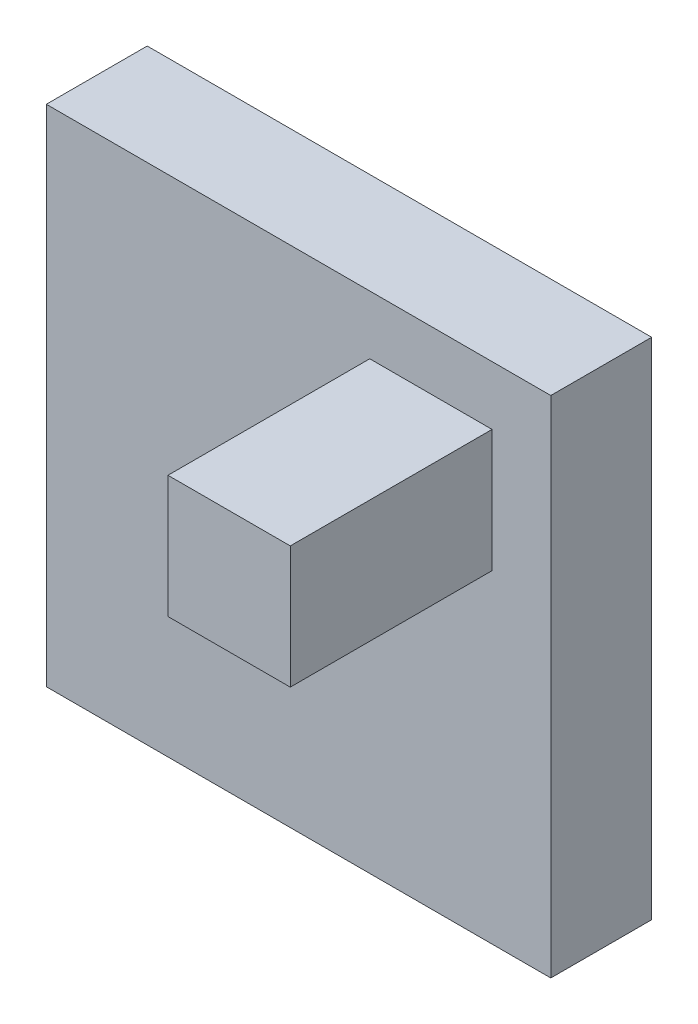
SolidWorks part; units mm, degrees
ref_plane "Front Plane" through (0, 0, 0) normal (0, 0, 1) x (1, 0, 0)
ref_plane "Top Plane" through (0, 0, 0) normal (0, 1, 0) x (1, 0, 0)
ref_plane "Right Plane" through (0, 0, 0) normal (1, 0, 0) x (0, 0, -1)
sketch "Sketch1" plane through (0, 0, 0) normal (0, 0, 1) x (1, 0, 0)
  line L1 (0, 0) -> (10, 0)
  line L2 (0, 0) -> (0, -10)
  line L3 (0, -10) -> (10, -10)
  line L4 (10, 0) -> (10, -10)
  dimension "D1" = 10
extrude "Boss-Extrude1" add sketch "Sketch1" along normal blind 2
sketch "Sketch2" plane through (0, 0, 2) normal (0, 0, 1) x (1, 0, 0)
  line L0 (6.4113, -1.1639) -> (6.4113, 0) construction
  line L1 (6.4113, -1.1639) -> (8.8361, -1.1639)
  line L2 (6.4113, -1.1639) -> (6.4113, -3.5887)
  line L3 (6.4113, -3.5887) -> (8.8361, -3.5887)
  line L4 (8.8361, -1.1639) -> (8.8361, -3.5887)
  line L5 (10, 0) -> (0, 0) construction
  line L6 (8.8361, -1.1639) -> (10, -1.1639) construction
  line L7 (10, -10) -> (10, 0) construction
  point P7 (6.4113, -3.5887)
extrude "Boss-Extrude2" add sketch "Sketch2" along normal blind 4
